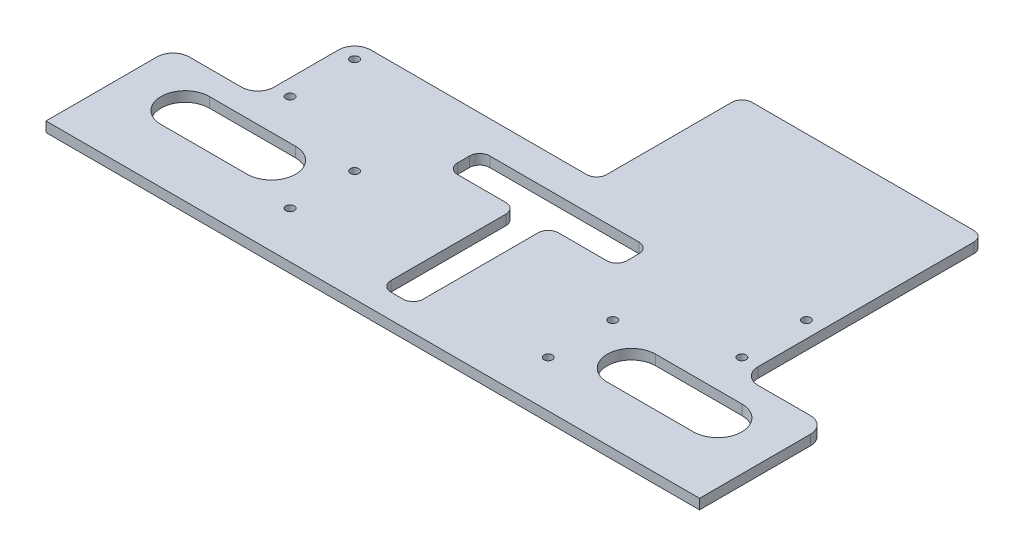
SolidWorks part; units mm, degrees
ref_plane "Front Plane" through (0, 0, 0) normal (0, 0, 1) x (1, 0, 0)
ref_plane "Top Plane" through (0, 0, 0) normal (0, 1, 0) x (1, 0, 0)
ref_plane "Right Plane" through (0, 0, 0) normal (1, 0, 0) x (0, 0, -1)
sketch "Sketch1" plane through (0, 0, 0) normal (0, 1, 0) x (1, 0, 0)
  line L0 (0, 0) -> (0, -141.8487) construction
  line L1 (-112, 57.5) -> (-5, 57.5)
  line L2 (-162, 1.5) -> (-162, -57.5)
  line L3 (-162, -57.5) -> (162, -57.5)
  line L4 (162, 1.5) -> (162, -57.5)
  line L5 (-162, 57.5) -> (162, -57.5) construction
  line L6 (-162, -57.5) -> (162, 57.5) construction
  line L7 (8, 20.5) -> (8, -36.5)
  line L8 (-37, 41.5) -> (37, 41.5)
  line L9 (-42, 36.5) -> (-42, 30.5)
  line L10 (-37, 25.5) -> (-13, 25.5)
  line L11 (42, 36.5) -> (42, 30.5)
  line L12 (-42, 41.5) -> (42, 25.5) construction
  line L13 (-42, 25.5) -> (42, 41.5) construction
  line L14 (3, -41.5) -> (-3, -41.5)
  line L15 (-8, 20.5) -> (-8, -36.5)
  line L16 (13, 25.5) -> (37, 25.5)
  line L17 (132, -14.5) -> (89.2478, -14.5) construction
  line L18 (132, -26.5) -> (89.2478, -26.5)
  line L19 (132, -2.5) -> (89.2478, -2.5)
  line L20 (-128, 9.5) -> (-154, 9.5)
  line L21 (-120, 49.5) -> (-120, 17.5)
  line L22 (-132, -14.5) -> (-89.2478, -14.5) construction
  line L23 (-132, -26.5) -> (-89.2478, -26.5)
  line L24 (-132, -2.5) -> (-89.2478, -2.5)
  line L25 (128, 9.5) -> (154, 9.5)
  line L26 (120, 49.5) -> (120, 17.5)
  line L27 (0, 62.5) -> (0, 124.5)
  line L28 (5, 129.5) -> (115, 129.5)
  line L29 (120, 124.5) -> (120, 49.5)
  circle A0 centre (112, 49.5) radius 2.1
  circle A1 centre (112, 17.5) radius 2.1
  circle A2 centre (64, -30.5) radius 2.1
  circle A3 centre (64, 1.5) radius 2.1
  circle A4 centre (-112, 17.5) radius 2.1
  circle A5 centre (-112, 49.5) radius 2.1
  circle A6 centre (-64, 1.5) radius 2.1
  circle A7 centre (-64, -30.5) radius 2.1
  arc A9 (132, -26.5) -> (132, -2.5) centre (132, -14.5) ccw
  arc A10 (89.2478, -2.5) -> (89.2478, -26.5) centre (89.2478, -14.5) ccw
  arc A11 (-112, 57.5) -> (-120, 49.5) centre (-112, 49.5) ccw
  arc A13 (-120, 17.5) -> (-128, 9.5) centre (-128, 17.5) cw
  arc A14 (-162, 1.5) -> (-154, 9.5) centre (-154, 1.5) cw
  arc A15 (-132, -26.5) -> (-132, -2.5) centre (-132, -14.5) cw
  arc A16 (-89.2478, -2.5) -> (-89.2478, -26.5) centre (-89.2478, -14.5) cw
  arc A17 (162, 1.5) -> (154, 9.5) centre (154, 1.5) ccw
  arc A19 (120, 17.5) -> (128, 9.5) centre (128, 17.5) ccw
  arc A20 (3, -41.5) -> (8, -36.5) centre (3, -36.5) ccw
  arc A21 (-3, -41.5) -> (-8, -36.5) centre (-3, -36.5) cw
  arc A22 (42, 36.5) -> (37, 41.5) centre (37, 36.5) ccw
  arc A23 (42, 30.5) -> (37, 25.5) centre (37, 30.5) cw
  arc A24 (-37, 25.5) -> (-42, 30.5) centre (-37, 30.5) cw
  arc A25 (-42, 36.5) -> (-37, 41.5) centre (-37, 36.5) cw
  arc A26 (8, 20.5) -> (13, 25.5) centre (13, 20.5) cw
  arc A27 (-8, 20.5) -> (-13, 25.5) centre (-13, 20.5) ccw
  arc A28 (0, 62.5) -> (-5, 57.5) centre (-5, 62.5) cw
  arc A29 (5, 129.5) -> (0, 124.5) centre (5, 124.5) ccw
  arc A30 (115, 129.5) -> (120, 124.5) centre (115, 124.5) cw
  point P0 (0, 0)
  point P6 (0, 57.5)
  point P7 (112, 57.5)
  point P10 (0, -57.5)
  point P13 (64, -57.5)
  point P19 (42, 33.5)
  point P32 (0, 33.5)
  point P38 (0, -41.5)
  point P41 (110.6239, -14.5)
  point P46 (-162, -19.4)
  point P57 (-110.6239, -14.5)
  point P73 (8, -41.5)
  point P76 (-8, -41.5)
  point P91 (8, 25.5)
  point P94 (-8, 25.5)
  point P98 (0, 57.5)
  point P101 (0, 129.5)
  dimension "D6" = 4.2
  dimension "D17" = 12
  dimension "D19" = 8
  dimension "D20" = 8
  dimension "D21" = 5
  dimension "D22" = 5
  dimension "D23" = 5
  dimension "D24" = 5
  dimension "D2" = 115
  dimension "D3" = 112
  dimension "D4" = 8
  dimension "D5" = 32
  dimension "D7" = 64
  dimension "D8" = 88
  dimension "D9" = 32
  dimension "D10" = 16
  dimension "D11" = 42
  dimension "D12" = 16
  dimension "D13" = 8
  dimension "D14" = 16
  dimension "D15" = 72
  dimension "D16" = 30
  dimension "D18" = 38.1
  dimension "D25" = 72
extrude "Boss-Extrude2" add sketch "Sketch1" along normal blind 5
sketch "Sketch2" plane through (0, 5, 0) normal (0, 1, 0) x (1, 0, 0)
  line L0 (162, -57.5) -> (162, 1.5) construction
  line L1 (-162, -57.5) -> (162, -57.5)
  line L2 (-162, -57.5) -> (-162, -53.5)
  line L3 (-162, -53.5) -> (162, -53.5)
  line L4 (162, -57.5) -> (162, -53.5)
  dimension "D1" = 4
extrude "Cut-Extrude1" cut sketch "Sketch2" against normal through all both and the other way through all
